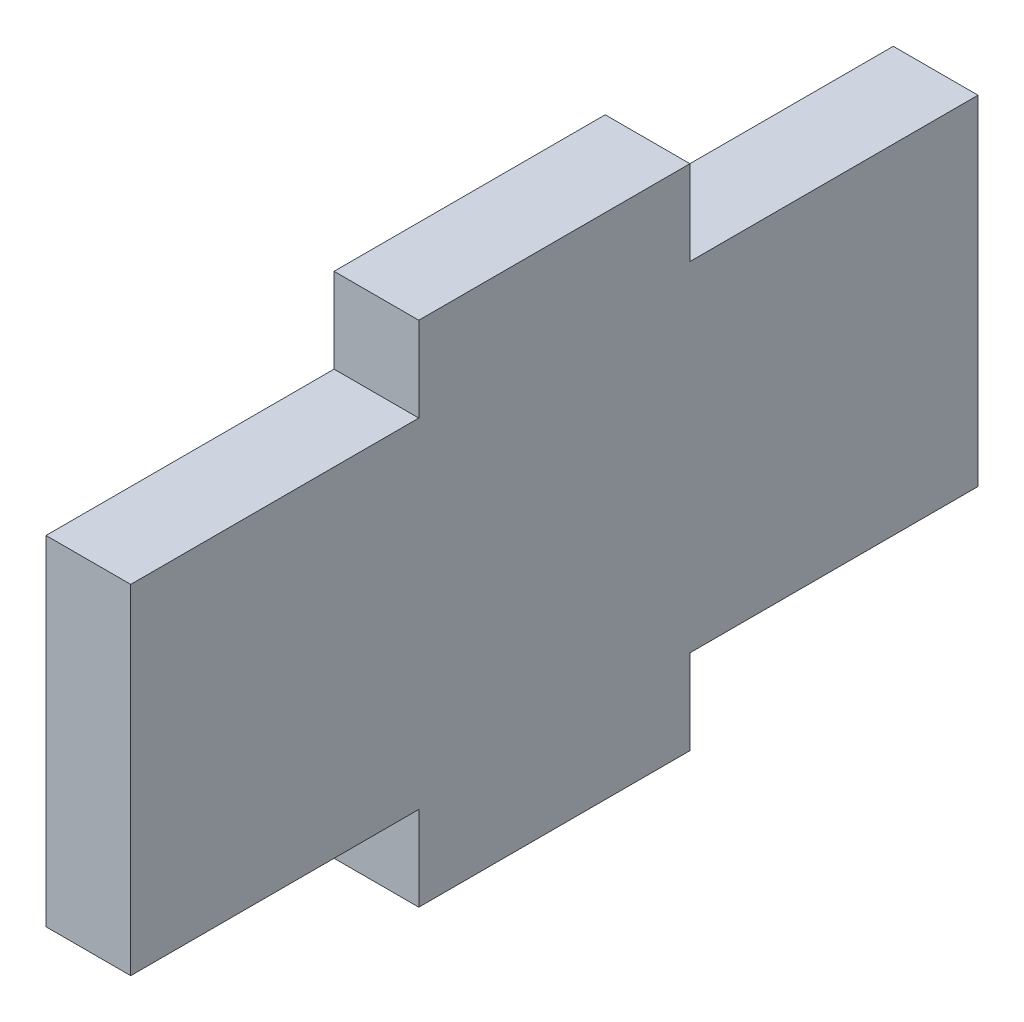
SolidWorks part; units mm, degrees
ref_plane "Front Plane" through (0, 0, 0) normal (0, 0, 1) x (1, 0, 0)
ref_plane "Top Plane" through (0, 0, 0) normal (0, 1, 0) x (1, 0, 0)
ref_plane "Right Plane" through (0, 0, 0) normal (1, 0, 0) x (0, 0, -1)
sketch "Sketch1" plane through (0, 0, 0) normal (1, 0, 0) x (0, 0, -1)
  line L0 (0, 13.0841) -> (0, -19.9065) construction
  line L1 (-25.7009, 0) -> (24.9533, 0) construction
  line L2 (-8, 10) -> (-8, 15)
  line L3 (-20, 10) -> (-8, 10)
  line L5 (-20, -10) -> (-8, -10)
  line L7 (-20, 10) -> (20, -10) construction
  line L8 (-20, -10) -> (20, 10) construction
  line L9 (-8, 15) -> (8, 15)
  line L10 (8, 15) -> (8, 10)
  line L11 (-8, -10) -> (-8, -15)
  line L12 (-8, -15) -> (8, -15)
  line L13 (8, -15) -> (8, -10)
  line L14 (8, 10) -> (20, 10)
  line L15 (8, -10) -> (20, -10)
  line L16 (20, 10) -> (25, 10)
  line L17 (25, 10) -> (25, -10)
  line L18 (25, -10) -> (20, -10)
  line L19 (-20, 10) -> (-25, 10)
  line L20 (-25, 10) -> (-25, -10)
  line L21 (-25, -10) -> (-20, -10)
  point P5 (0, 0)
  dimension "D1" = 20
  dimension "D2" = 40
  dimension "D3" = 16
  dimension "D4" = 16
  dimension "D5" = 5
  dimension "D6" = 5
  dimension "D7" = 5
  dimension "D8" = 5
extrude "Boss-Extrude1" add sketch "Sketch1" along normal blind 5
